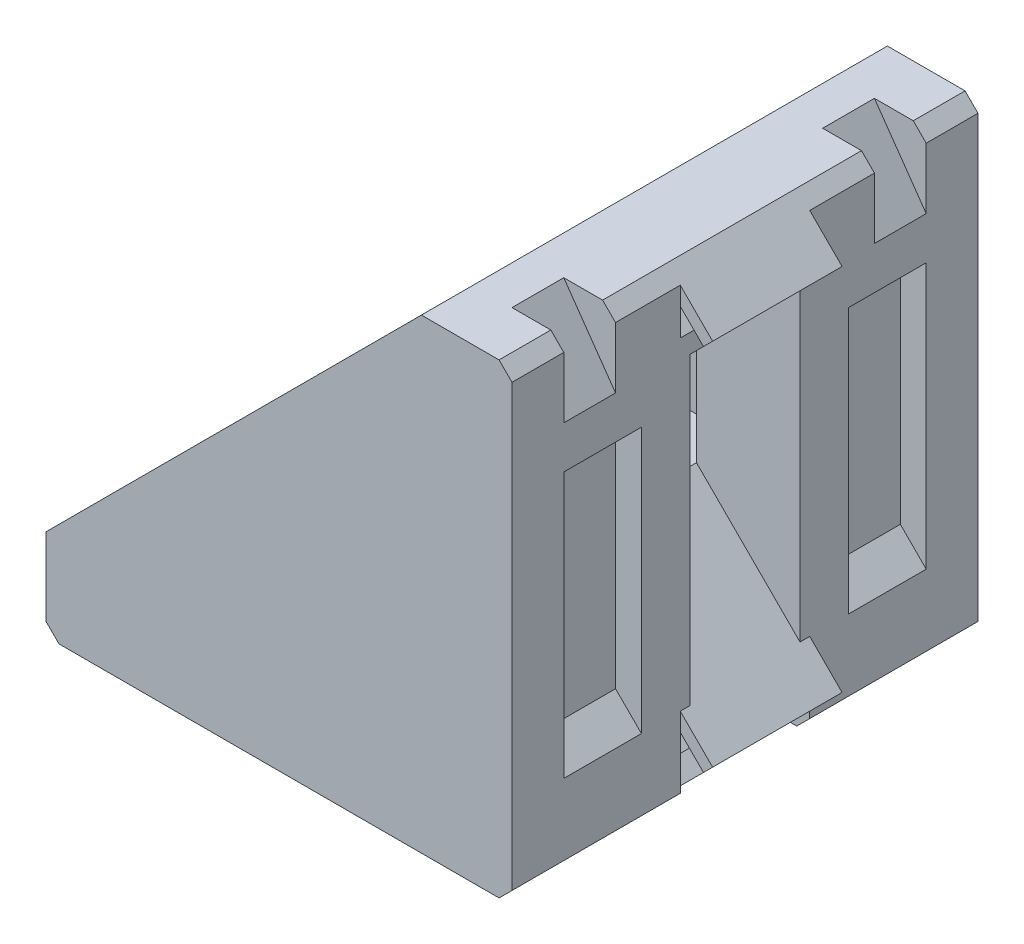
SolidWorks part; units mm, degrees
ref_plane "前视基准面" through (0, 0, 0) normal (0, 0, 1) x (1, 0, 0)
ref_plane "上视基准面" through (0, 0, 0) normal (0, 1, 0) x (1, 0, 0)
ref_plane "右视基准面" through (0, 0, 0) normal (1, 0, 0) x (0, 0, -1)
sketch "草图1" plane through (0, 0, 0) normal (0, 0, 1) x (1, 0, 0)
  line L1 (21.5, 95.4326) -> (27.5, 89.4326)
  line L2 (6, 87.4326) -> (6, 95.4326)
  line L3 (28, 117.4326) -> (36, 117.4326)
  line L4 (34, 95.9326) -> (28, 101.9326)
  line L5 (38.5, 119.9326) -> (37.7929, 119.2255)
  line L6 (37.7929, 119.2255) -> (36, 121.0184)
  line L7 (36, 93.9326) -> (38.5, 91.4326)
  line L8 (38.5, 91.4326) -> (37.7929, 90.7255)
  line L9 (37.7929, 90.7255) -> (36, 92.5184)
  line L10 (30.9142, 87.4326) -> (32.7071, 85.6397)
  line L11 (32.7071, 85.6397) -> (32, 84.9326)
  line L12 (32, 84.9326) -> (29.5, 87.4326)
  line L13 (2.4142, 87.4326) -> (4.2071, 85.6397)
  line L14 (4.2071, 85.6397) -> (3.5, 84.9326)
  line L15 (35.2929, 93.2255) -> (36, 92.5184)
  line L16 (33.8106, 91.7433) -> (35.2929, 93.2255)
  line L17 (35.2249, 90.3291) -> (33.8106, 91.7433)
  line L18 (33.1035, 88.2077) -> (35.2249, 90.3291)
  line L19 (31.6893, 89.6219) -> (33.1035, 88.2077)
  line L20 (30.2071, 88.1397) -> (31.6893, 89.6219)
  line L21 (30.9142, 87.4326) -> (30.2071, 88.1397)
  line L22 (1, 95.4326) -> (6, 95.4326)
  line L23 (28, 95.4326) -> (28, 101.9326)
  line L24 (0, 88.4326) -> (0, 94.4326)
  line L25 (0, 94.4326) -> (1, 95.4326)
  line L26 (29, 123.4326) -> (35, 123.4326)
  line L28 (1, 87.4326) -> (0, 88.4326)
  line L29 (2.4142, 87.4326) -> (1.7071, 88.1397)
  line L30 (1.7071, 88.1397) -> (2.7678, 89.2004)
  line L31 (2.7678, 89.2004) -> (4.5355, 87.4326)
  line L32 (35.2929, 121.7255) -> (36, 121.0184)
  line L33 (36, 118.8971) -> (34.2322, 120.6648)
  line L34 (34.2322, 120.6648) -> (35.2929, 121.7255)
  line L35 (35, 123.4326) -> (36, 122.4326)
  line L39 (6, 87.4326) -> (4.5355, 87.4326)
  line L40 (36, 122.4326) -> (38.5, 119.9326)
  line L41 (3.5, 84.9326) -> (1, 87.4326)
  line L42 (34, 95.9326) -> (36, 93.9326)
  line L45 (27.5, 89.4326) -> (29.5, 87.4326)
  line L46 (21.5, 95.4326) -> (28, 95.4326)
  line L47 (28, 122.4326) -> (29, 123.4326)
  line L48 (28, 117.4326) -> (28, 122.4326)
  line L49 (36, 118.8971) -> (36, 117.4326)
extrude "拉伸1" add sketch "草图1" along normal blind 5
sketch "草图2" plane through (0, 0, 5) normal (0, 0, 1) x (1, 0, 0)
  line L0 (35, 123.4326) -> (29, 123.4326)
  line L1 (29, 123.4326) -> (28, 122.4326)
  line L2 (28, 122.4326) -> (28, 95.4326)
  line L3 (28, 95.4326) -> (1, 95.4326)
  line L4 (1, 95.4326) -> (0, 94.4326)
  line L5 (0, 94.4326) -> (0, 88.4326)
  line L6 (0, 88.4326) -> (1, 87.4326)
  line L7 (35, 123.4326) -> (36, 122.4326)
  line L8 (36, 122.4326) -> (36, 87.4326)
  line L9 (1, 87.4326) -> (36, 87.4326)
extrude "拉伸2" add sketch "草图2" along normal blind 13
sketch "草图3" plane through (0, 0, 5) normal (0, 0, -1) x (-1, 0, 0)
  line L0 (-28, 117.4326) -> (-36, 117.4326)
  line L1 (-36, 117.4326) -> (-36, 93.9326)
  line L2 (-36, 93.9326) -> (-28, 101.9326)
  line L3 (-28, 101.9326) -> (-28, 117.4326)
extrude "拉伸3" add sketch "草图3" along normal blind 0.75
ref_plane "基准面4" through (61.7163, 61.7163, 0) normal (-0.7071, -0.7071, 0) x (0, 0, 1)
mirror "镜向1" about plane through (61.7163, 61.7163, 0) normal (-0.7071, -0.7071, 0) of "拉伸3"
ref_plane "基准面5" through (0, 0, 14) normal (0, 0, 1) x (1, 0, 0)
sketch "草图4" plane through (0, 0, 14) normal (0, 0, 1) x (1, 0, 0)
  line L0 (34, 114.4326) -> (36, 114.4326)
  line L1 (36, 87.4326) -> (36, 122.4326) construction
  line L2 (35, 123.4326) -> (29, 123.4326) construction
  line L3 (36, 93.9326) -> (36, 114.4326)
  line L4 (34, 114.4326) -> (34, 95.9326)
  line L5 (34, 95.9326) -> (36, 93.9326)
  dimension "D1" = 2
  dimension "D2" = 9
  dimension "D3" = 18.5
extrude "切除-拉伸1" cut sketch "草图4" against normal blind 6
sketch "草图6" plane through (0, 0, 14) normal (0, 0, 1) x (1, 0, 0)
  line L0 (32, 123.4326) -> (35, 123.4326)
  line L1 (35, 123.4326) -> (36, 122.4326)
  line L2 (36, 122.4326) -> (36, 117.72)
  line L4 (32, 123.4326) -> (36, 117.72)
  dimension "D1" = 4
  dimension "D2" = 55
extrude "切除-拉伸2" cut sketch "草图6" against normal blind 4
mirror "镜向2" about plane through (61.7163, 61.7163, 0) normal (-0.7071, -0.7071, 0) of "切除-拉伸2", "切除-拉伸1"
ref_plane "基准面6" through (0, 0, 0) normal (0, 0, -1) x (-1, 0, 0)
sketch "草图7" plane through (0, 0, 18) normal (0, 0, 1) x (1, 0, 0)
  line L0 (1, 95.4326) -> (28, 95.4326)
  line L1 (28, 95.4326) -> (28, 122.4326)
  line L2 (28, 122.4326) -> (1, 95.4326)
extrude "拉伸5" add sketch "草图7" against normal blind 4
mirror "镜向4" about plane through (0, 0, 0) normal (0, 0, -1) of bodies 112
chamfer "倒角1" distance 1 angle 45 2 edges at (36, 87.4326, 11.5) (36, 87.4326, -11.5)
